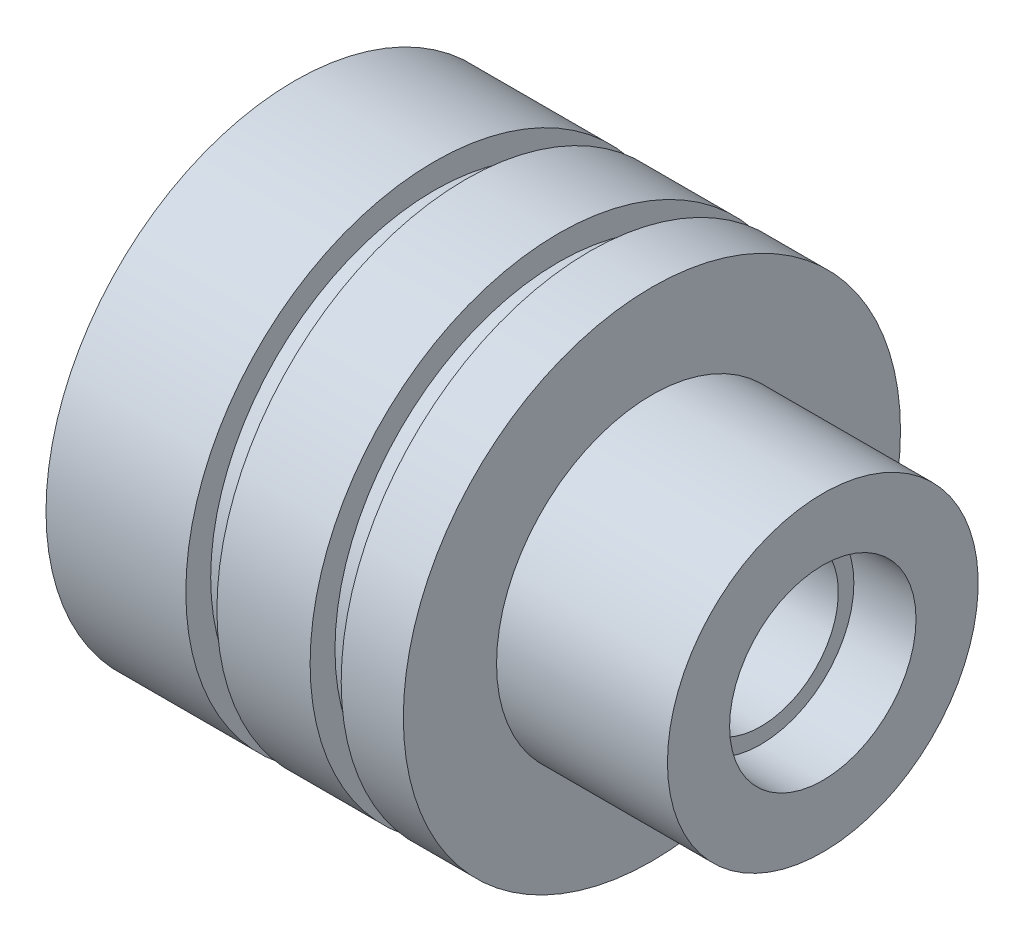
SolidWorks part; units mm, degrees
ref_plane "Ebene vorne" through (0, 0, 0) normal (0, 0, 1) x (1, 0, 0)
ref_plane "Ebene oben" through (0, 0, 0) normal (0, 1, 0) x (1, 0, 0)
ref_plane "Ebene rechts" through (0, 0, 0) normal (1, 0, 0) x (0, 0, -1)
sketch "Skizze1" plane through (0, 0, 0) normal (0, 0, 1) x (1, 0, 0)
  line L0 (0, 0) -> (17, 0) construction
  line L1 (0, 8) -> (0, 2.5)
  line L2 (0, 8) -> (4.5, 8)
  line L3 (4.5, 8) -> (4.5, 7.2)
  line L4 (4.5, 7.2) -> (5.5, 7.2)
  line L5 (5.5, 7.2) -> (5.5, 8)
  line L6 (5.5, 8) -> (8.5, 8)
  line L7 (8.5, 8) -> (8.5, 7.2)
  line L8 (8.5, 7.2) -> (9.5, 7.2)
  line L9 (9.5, 7.2) -> (9.5, 8)
  line L10 (9.5, 8) -> (11.5, 8)
  line L11 (0, 2.5) -> (15, 2.5)
  line L12 (15, 2.5) -> (15, 3)
  line L13 (15, 3) -> (17, 3)
  line L14 (17, 3) -> (17, 5)
  line L15 (17, 5) -> (11.5, 5)
  line L16 (11.5, 5) -> (11.5, 8)
  line L17 (0, 0) -> (0, 2.5) construction
  line L18 (17, 0) -> (17, 3) construction
  dimension "D1" = 17
  dimension "D2" = 5
  dimension "D3" = 2
  dimension "D4" = 16
  dimension "D5" = 10
  dimension "D6" = 6
  dimension "D7" = 5.5
  dimension "D8" = 0.8
  dimension "D9" = 1
  dimension "D10" = 2
  dimension "D11" = 6
  dimension "D12" = 1
revolve "Rotation1" add sketch "Skizze1" angle 360 about L0
